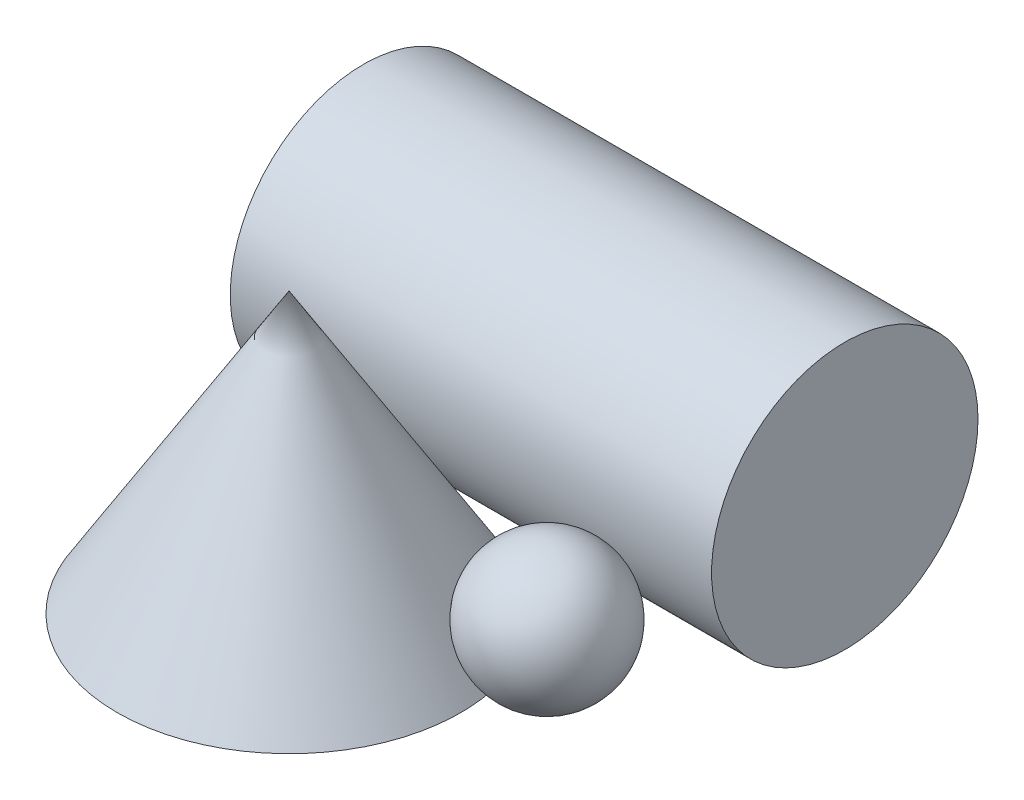
SolidWorks part; units mm, degrees
ref_plane "Front" through (0, 0, 0) normal (0, 0, 1) x (1, 0, 0)
ref_plane "Top" through (0, 0, 0) normal (0, 1, 0) x (1, 0, 0)
ref_plane "Right" through (0, 0, 0) normal (1, 0, 0) x (0, 0, -1)
sketch "Sketch1" plane through (0, 0, 0) normal (0, 0, 1) x (1, 0, 0)
  line L0 (40, 0) -> (0, 0)
  line L1 (0, 0) -> (0, 65)
  line L2 (0, 65) -> (40, 0)
  line L3 (40, 0) -> (39.6304, 1.1087)
  dimension "D1" = 40
  dimension "D2" = 65
revolve "Revolve1" add sketch "Sketch1" angle 360 about L1
sketch "Sketch2" plane through (0, 0, 0) normal (1, 0, 0) x (0, 0, -1)
  circle A0 centre (57.3227, 31) radius 31
extrude "Extrude1" add sketch "Sketch2" along normal blind 72 and the other way blind 40 separate body
sketch "Sketch3" plane through (72, 0, 0) normal (1, 0, 0) x (0, 0, -1)
  circle A2 centre (12.7805, 16) radius 16 construction
ref_plane "Plane1" through (0, 16, 0) normal (0, 1, 0) x (-1, 0, 0)
sketch "Sketch5" plane through (0, 0, 0) normal (1, 0, 0) x (0, 0, -1)
  circle A0 centre (-48.9407, 16) radius 16 construction
sketch "Sketch6" plane through (0, 16, 0) normal (0, 1, 0) x (-1, 0, 0)
  line L0 (-63.2425, -12.7805) -> (-31.2425, -12.7805)
  arc A1 (-63.2425, -12.7805) -> (-31.2425, -12.7805) centre (-47.2425, -12.7805) ccw
revolve "Revolve2" add sketch "Sketch6" angle 360 about L0
